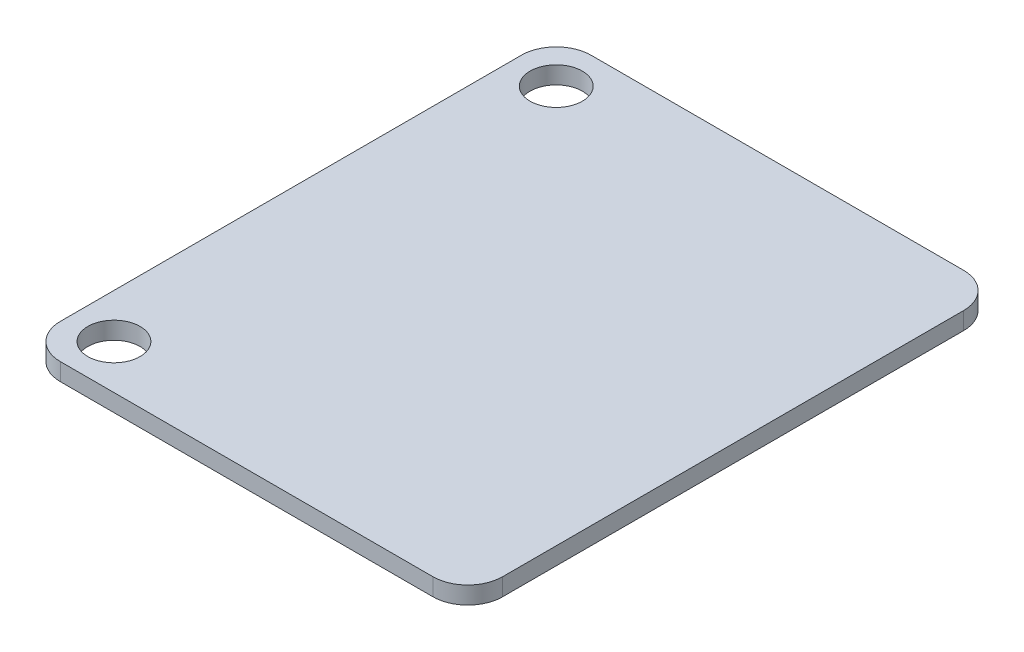
SolidWorks part; units mm, degrees
ref_plane "Front Plane" through (0, 0, 0) normal (0, 0, 1) x (1, 0, 0)
ref_plane "Top Plane" through (0, 0, 0) normal (0, 1, 0) x (1, 0, 0)
ref_plane "Right Plane" through (0, 0, 0) normal (1, 0, 0) x (0, 0, -1)
sketch "Sketch1" plane through (0, 0, 0) normal (0, 1, 0) x (1, 0, 0)
  line L1 (-12.52, -14.186) -> (12.88, -14.186)
  line L2 (-12.52, -14.186) -> (-12.52, 16.294)
  line L3 (-12.52, 16.294) -> (12.88, 16.294)
  line L4 (12.88, -14.186) -> (12.88, 16.294)
  circle A0 centre (-9.98, 13.754) radius 1.5
  circle A3 centre (-9.98, -11.646) radius 1.5
  dimension "D4" = 3
  dimension "D5" = 3
  dimension "D6" = 2.54
  dimension "D7" = 2.54
  dimension "D8" = 2.54
  dimension "D1" = 30.48
  dimension "D2" = 25.4
  dimension "D3" = 25.4
extrude "Boss-Extrude1" add sketch "Sketch1" along normal blind 1
fillet "Fillet1" radius 2 1 edges at (-12.52, 0.5, 14.186)
fillet "Fillet2" radius 2 1 edges at (12.88, 0.5, 14.186)
fillet "Fillet3" radius 2 1 edges at (12.88, 0.5, -16.294)
fillet "Fillet4" radius 2 1 edges at (-12.52, 0.5, -16.294)
